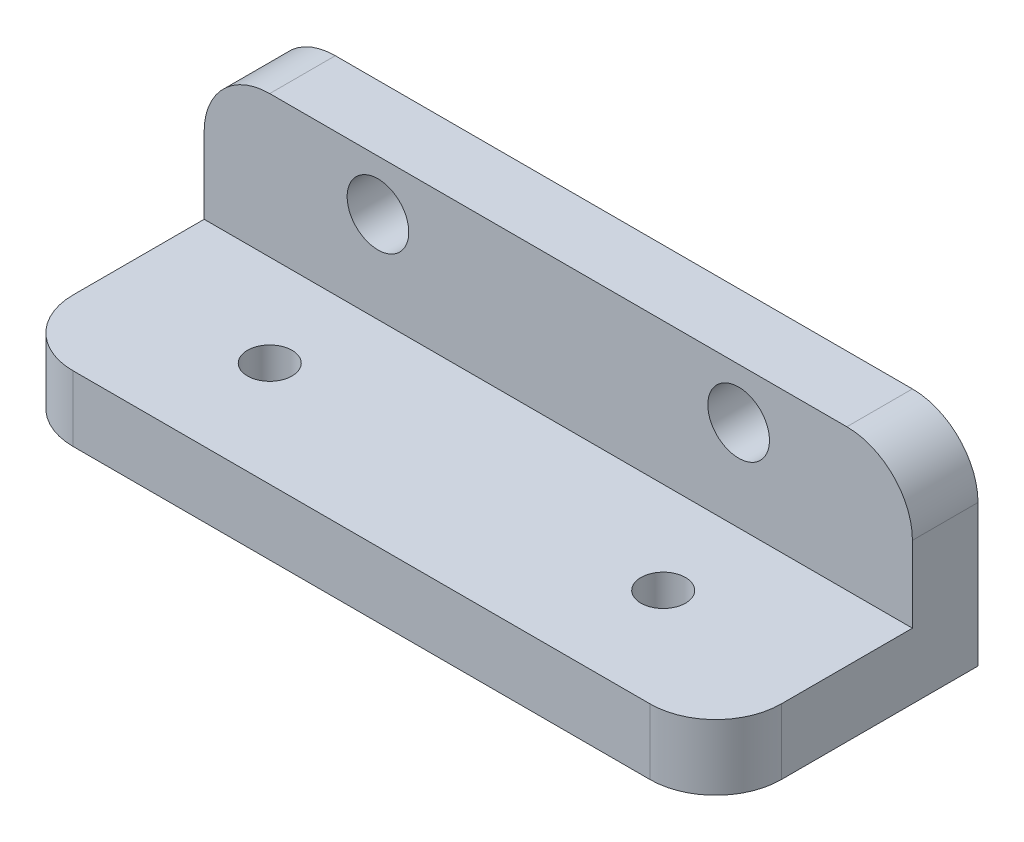
SolidWorks part; units mm, degrees
ref_plane "Front Plane" through (0, 0, 0) normal (0, 0, 1) x (1, 0, 0)
ref_plane "Top Plane" through (0, 0, 0) normal (0, 1, 0) x (1, 0, 0)
ref_plane "Right Plane" through (0, 0, 0) normal (1, 0, 0) x (0, 0, -1)
sketch "Sketch1" plane through (0, 0, 0) normal (0, 1, 0) x (1, 0, 0)
  line L1 (27, -10) -> (-27, -10)
  line L2 (27, -10) -> (27, 10)
  line L3 (27, 10) -> (-27, 10)
  line L4 (-27, -10) -> (-27, 10)
  line L5 (27, -10) -> (-27, 10) construction
  line L6 (27, 10) -> (-27, -10) construction
  point P0 (0, 0)
  dimension "D1" = 54
  dimension "D2" = 20
extrude "Boss-Extrude1" add sketch "Sketch1" along normal blind 5
sketch "Sketch2" plane through (0, 5, 0) normal (0, 1, 0) x (1, 0, 0)
  line L0 (27, -10) -> (27, 10) construction
  line L1 (-27, 10) -> (27, 10)
  line L2 (-27, 10) -> (-27, 5)
  line L3 (-27, 5) -> (27, 5)
  line L4 (27, 10) -> (27, 5)
  dimension "D1" = 5
extrude "Boss-Extrude2" add sketch "Sketch2" along normal blind 10.8
hole_wizard "M3 Clearance Hole1" positions "Sketch4" profile "Sketch3" hole size "M3" standard "ANSI Metric"
sketch "Sketch4" plane through (0, 0, -5) normal (0, 0, 1) x (1, 0, 0)
  line L0 (-27, 15.8) -> (27, 15.8) construction
  line L1 (27, 15.8) -> (27, 5) construction
  point P0 (-13.75, 12.6)
  point P2 (13.75, 12.6)
  dimension "D1" = 3.2
  dimension "D2" = 3.2
  dimension "D3" = 13.25
  dimension "D4" = 27.5
sketch "Sketch3" plane through (-13.75, 12.6, -5) normal (1, 0, 0) x (0, -1, 0)
  line L0 (0, 0) -> (0, 29.7315)
  line L1 (0, 29.7315) -> (1.7, 28.71)
  line L2 (1.7, 28.71) -> (1.7, 0)
  line L5 (1.7, 0) -> (0, 0)
  line L10 (0, 29.7315) -> (-1.7, 28.71) construction
  line L11 (0, -6.35) -> (0, 107.95) construction
  dimension "Hole Dia." = 3.4
  dimension "Hole Depth" = 28.71
  dimension "Drill Angle" = 118
hole_wizard "M3 Clearance Hole2" positions "Sketch8" profile "Sketch7" hole size "M3" standard "ANSI Metric" end condition through all
sketch "Sketch8" plane through (0, 5, 0) normal (0, 1, 0) x (1, 0, 0)
  line L0 (-27, -10) -> (27, -10) construction
  line L1 (-27, 5) -> (-27, -10) construction
  point P0 (15, -2)
  point P2 (-15, -2)
  dimension "D1" = 8
  dimension "D2" = 8
  dimension "D3" = 30
  dimension "D4" = 12
sketch "Sketch7" plane through (15, 5, 2) normal (1, 0, 0) x (0, 0, 1)
  line L0 (0, 0) -> (0, 5)
  line L1 (0, 5) -> (1.7, 5)
  line L2 (1.7, 5) -> (1.7, 0)
  line L5 (1.7, 0) -> (0, 0)
  line L11 (0, -6.35) -> (0, 107.95) construction
  dimension "Thru Hole Dia." = 3.4
  dimension "Thru Hole Depth" = 5
fillet "Fillet1" radius 5 4 edges at (27, 2.5, 10) (-27, 2.5, 10) (27, 15.8, -7.5) (-27, 15.8, -7.5)
sketch "Sketch9" plane through (0, 0, -10) normal (0, 0, -1) x (-1, 0, 0)
  line L2 (-22, 15.8) -> (22, 15.8) construction
  line L3 (27, 10.8) -> (27, 0) construction
  circle A0 centre (13.75, 11.95) radius 2.35
  dimension "D1" = 3.85
  dimension "D2" = 13.25
sketch "Sketch11" plane through (0, 0, -10) normal (0, 0, -1) x (-1, 0, 0)
  line L2 (-22, 15.8) -> (22, 15.8) construction
  line L3 (-27, 10.8) -> (-27, 0) construction
  circle A0 centre (-13.75, 11.95) radius 2.35
  dimension "D1" = 3.85
  dimension "D2" = 13.25
extrude "Cut-Extrude4" cut sketch "Sketch11" against normal blind 7.8
extrude "Cut-Extrude5" cut sketch "Sketch9" against normal blind 7.8 contours A0
